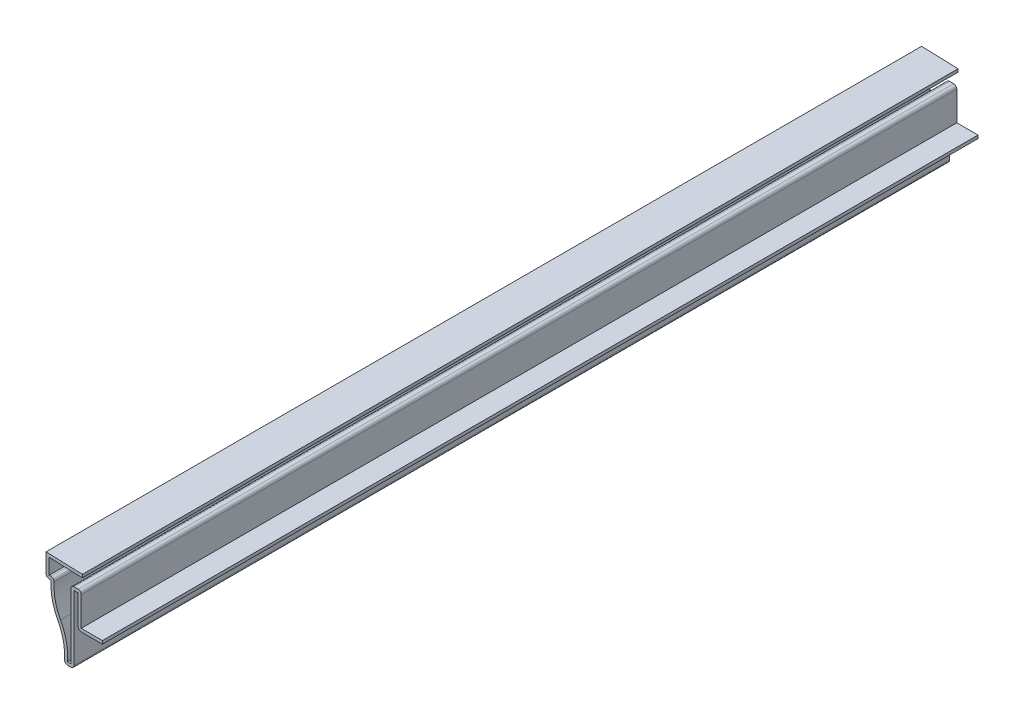
SolidWorks part; units mm, degrees
ref_plane "Front Plane" through (0, 0, 0) normal (0, 0, 1) x (1, 0, 0)
ref_plane "Top Plane" through (0, 0, 0) normal (0, 1, 0) x (1, 0, 0)
ref_plane "Right Plane" through (0, 0, 0) normal (1, 0, 0) x (0, 0, -1)
sketch "Sketch1" plane through (0, 0, 0) normal (0, 0, 1) x (1, 0, 0)
  line L0 (0, 0) -> (0, 22.225)
  line L1 (0, 22.225) -> (1.3462, 22.225)
  line L2 (1.3462, 22.225) -> (1.3462, 11.684)
  line L3 (1.3462, 11.684) -> (9.2837, 11.684)
  line L4 (0, 0) -> (-3.175, 0)
  line L5 (-7.5018, 21.4312) -> (-9.1281, 21.4312)
  line L6 (-9.1281, 21.4312) -> (-9.1281, 28.575)
  line L7 (-9.1281, 28.575) -> (2.7781, 28.1781)
  line L8 (2.3622, 12.7) -> (9.2837, 12.7)
  line L9 (2.3622, 23.241) -> (2.3622, 12.7)
  line L10 (-1.016, 23.241) -> (2.3622, 23.241)
  line L11 (-1.016, 1.016) -> (-1.016, 23.241)
  line L12 (-1.016, 1.016) -> (-2.0634, 1.016)
  line L13 (-6.3861, 22.4472) -> (-8.1121, 22.4472)
  line L14 (-8.1121, 22.4472) -> (-8.1121, 27.5246)
  line L15 (-8.1121, 27.5246) -> (2.7443, 27.1627)
  line L16 (9.2837, 11.684) -> (9.2837, 12.7)
  line L17 (2.7781, 28.1781) -> (2.7443, 27.1627)
  arc A0 (-3.175, 0) -> (-5.2909, 11.2353) centre (-22.0911, 2.2546) ccw
  arc A1 (-5.2909, 11.2353) -> (-7.5018, 21.4312) centre (11.5094, 20.2161) cw
  arc A2 (-2.0634, 1.016) -> (-4.3949, 11.7143) centre (-22.0911, 2.2546) ccw
  arc A3 (-4.3949, 11.7143) -> (-6.3861, 22.4472) centre (11.5094, 20.2161) cw
  point P11 (0, 0)
  point P15 (-15.24, 25.3795)
  point P16 (-13.1962, 24.8879)
  point P17 (-8.9719, 15.0556)
  point P31 (-5.6747, 16.8852)
  point P32 (-4.9689, 0)
  point P33 (-13.1715, 23.0128)
  point P34 (-16.256, 27.6463)
  point P35 (-15.6499, 28.575)
  point P36 (-11.6324, 21.5014)
  point P37 (-4.4497, 10.1717)
  point P38 (-6.005, 22.4472)
  point P39 (-4.3964, 11.684)
  point P40 (-8.576, 28.559)
  dimension "D2" = 19.05
  dimension "D6" = 4.3656
  dimension "D9" = 1.5875
  dimension "D1" = 28.575
  dimension "D4" = 1.3462
  dimension "D5" = 7.9375
  dimension "D7" = 0.3969
  dimension "D8" = 11.9062
  dimension "D10" = 9.1281
  dimension "D11" = 21.4312
  dimension "D12" = 7.1438
  dimension "D13" = 9.525
  dimension "D14" = 3.175
  dimension "D15" = 12.7
  dimension "D3" = 1.016
extrude "Boss-Extrude1" add sketch "Sketch1" against normal blind 285.75
fillet "Fillet1" radius 1.016 7 edges at (-3.175, 0, -142.875) (0, 0, -142.875) (1.3462, 11.684, -142.875) (2.3622, 23.241, -142.875) (-1.016, 23.241, -142.875) (-9.1281, 21.4312, -142.875) (-6.3861, 22.4472, -142.875)
